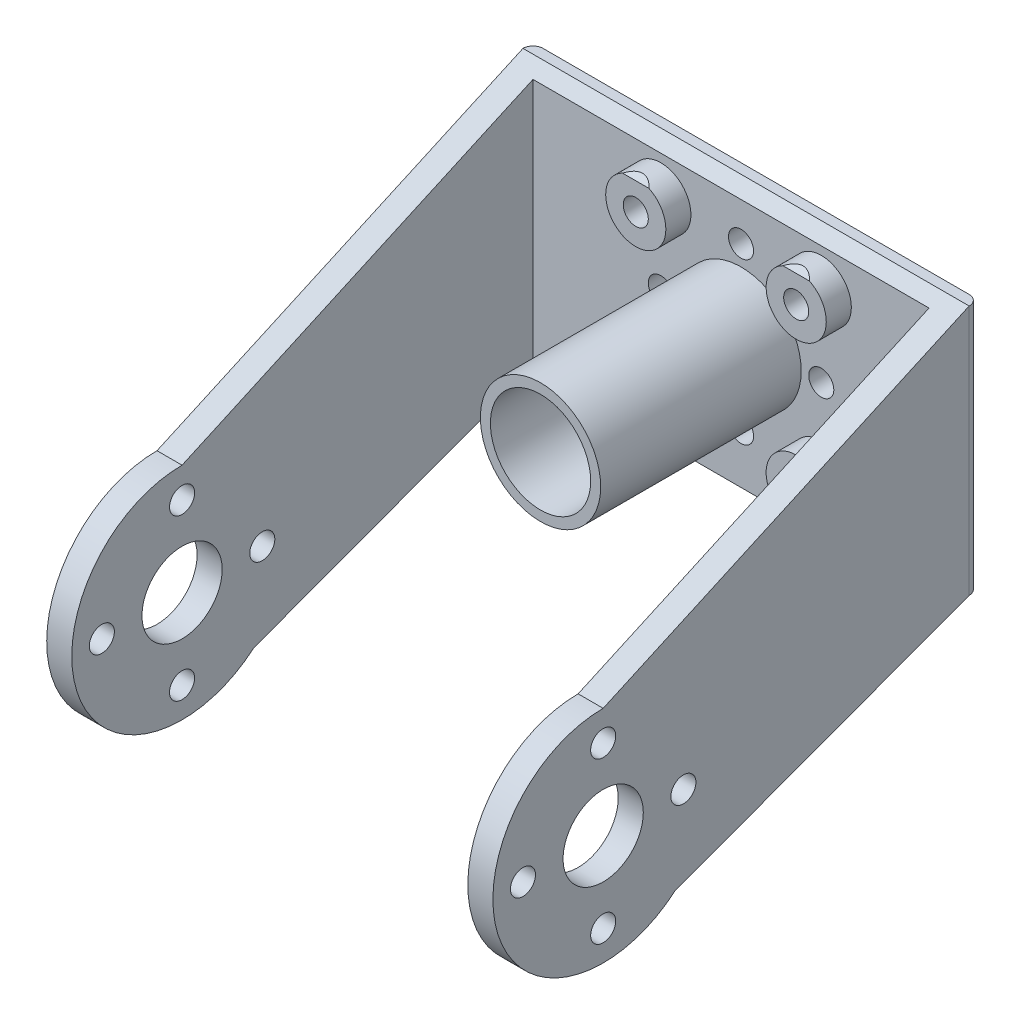
SolidWorks part; units mm, degrees
ref_plane "Front Plane" through (0, 0, 0) normal (0, 0, 1) x (1, 0, 0)
ref_plane "Top Plane" through (0, 0, 0) normal (0, 1, 0) x (1, 0, 0)
ref_plane "Right Plane" through (0, 0, 0) normal (1, 0, 0) x (0, 0, -1)
sketch "Sketch1" plane through (0, 0, 0) normal (0, 0, 1) x (1, 0, 0)
  line L1 (0, 0) -> (44.5, 0)
  line L2 (0, 0) -> (0, 40)
  line L3 (0, 40) -> (44.5, 40)
  line L4 (44.5, 0) -> (44.5, 40)
  dimension "D1" = 44.5
  dimension "D2" = 40
extrude "Boss-Extrude1" add sketch "Sketch1" along normal blind 48.5
sketch "Sketch2" plane through (0, 0, 48.5) normal (0, 0, 1) x (1, 0, 0)
  line L0 (0, 40) -> (0, 0) construction
  line L1 (2.5, 40) -> (42, 40)
  line L2 (2.5, 40) -> (2.5, 0)
  line L3 (2.5, 0) -> (42, 0)
  line L4 (42, 40) -> (42, 0)
  line L5 (0, 0) -> (44.5, 0) construction
  line L6 (44.5, 0) -> (44.5, 40) construction
  point P10 (42, 20)
  point P12 (0, 20)
  point P13 (2.5, 20)
  dimension "D1" = 2.5
  dimension "D2" = 40
  dimension "D3" = 2.5
extrude "Cut-Extrude1" cut sketch "Sketch2" against normal blind 46
fillet "Fillet1" radius 1 2 edges at (44.5, 20, 0) (0, 20, 0)
sketch "Sketch3" plane through (0, 0, 2.5) normal (0, 0, 1) x (1, 0, 0)
  line L0 (2.5, 40) -> (2.5, 0) construction
  line L3 (42, 40) -> (2.5, 40) construction
  circle A0 centre (15.25, 19.5) radius 3
  circle A1 centre (31.25, 19.5) radius 3
  circle A2 centre (31.25, 35.5) radius 3
  circle A3 centre (15.25, 35.5) radius 3
  dimension "D1" = 6
  dimension "D2" = 12.75
  dimension "D6" = 16
  dimension "D7" = 16
  dimension "D8" = 4.5
  dimension "D4" = 2
  dimension "D5" = 2
extrude "Boss-Extrude2" add sketch "Sketch3" along normal blind 2.5
sketch "Sketch5" plane through (0, 0, 5) normal (0, 0, 1) x (1, 0, 0)
  line L3 (42, 40) -> (2.5, 40) construction
  line L4 (2.5, 40) -> (2.5, 0) construction
  circle A1 centre (23.25, 35.5) radius 1.25
  circle A10 centre (31.25, 35.5) radius 1.25
  circle A11 centre (15.25, 35.5) radius 1.25
  circle A14 centre (23.25, 27.5) radius 5
  circle A15 centre (23.25, 27.5) radius 1.25 [skipped]
  circle A16 centre (31.25, 27.5) radius 1.25
  circle A17 centre (23.25, 19.5) radius 1.25
  circle A18 centre (31.25, 19.5) radius 1.25
  circle A19 centre (15.25, 27.5) radius 1.25
  circle A20 centre (15.25, 19.5) radius 1.25
  circle A21 centre (15.25, 35.5) radius 3 construction
  dimension "D1" = 2.5
  dimension "D2" = 4.5
  dimension "D7" = 3
  dimension "D8" = 3
  dimension "D9" = 8
  dimension "D4" = 10
  dimension "D3" = 12.75
  dimension "D5" = 12.5
  dimension "D6" = 20.75
extrude "Cut-Extrude5" cut sketch "Sketch5" against normal blind 6
sketch "Sketch7" plane through (44.5, 0, 0) normal (1, 0, 0) x (0, 0, -1)
  line L0 (-48.5, 0) -> (-1, 0) construction
  line L1 (-37.5, 1.5) -> (-1, 15)
  line L2 (-37.5, 23.5) -> (-1, 40)
  line L3 (-1, 0) -> (-1, 40) construction
  line L4 (-48.5, 0) -> (-48.5, 40) construction
  circle A0 centre (-37.5, 12.5) radius 4
  circle A1 centre (-37.5, 12.5) radius 11
  point P4 (0, 0)
  dimension "D2" = 8
  dimension "D4" = 22
  dimension "D1" = 12.5
  dimension "D3" = 25
  dimension "D5" = 11
extrude "Cut-Extrude7" cut sketch "Sketch7" against normal blind 44.5
sketch "Sketch8" plane through (44.5, 0, 0) normal (1, 0, 0) x (0, 0, -1)
  line L2 (-9, 23) -> (-4, 23) construction
  line L3 (-9, 32.5) -> (-9, 23) construction
  circle A7 centre (-37.5, 12.5) radius 8
  circle A8 centre (-45.5, 12.5) radius 1.25
  circle A9 centre (-37.5, 20.5) radius 1.25
  circle A11 centre (-37.5, 4.5) radius 1.25
  circle A12 centre (-29.5, 12.5) radius 1.25
  point P4 (-29.5, 12.5)
  point P9 (0, 0)
  point P11 (-27.5, 4.5)
  point P24 (-37.5, 20.5)
  point P25 (-45.5, 12.5)
  circle M8 centre (-37.5, 12.5) radius 4
  dimension "D1" = 2.5
  dimension "D6" = 2.5
  dimension "D5" = 2.5
  dimension "D3" = 16
  dimension "D2" = 16
  dimension "D4" = 2.5
extrude "Cut-Extrude8" cut sketch "Sketch8" against normal blind 44.5 contours A12 A7 A9 A8 A11 M8
sketch "Sketch9" plane through (0, 0, 1) normal (0, 0, 1) x (1, 0, 0)
  line L1 (44.5, 15) -> (0, 15)
  line L2 (44.5, 15) -> (44.5, 0)
  line L3 (44.5, 0) -> (0, 0)
  line L4 (0, 15) -> (0, 0)
extrude "Cut-Extrude9" cut sketch "Sketch9" against normal blind 10
sketch "Sketch10" plane through (0, 0, 2.5) normal (0, 0, 1) x (1, 0, 0)
  circle A0 centre (23.25, 27.5) radius 5
extrude "Extrude-Thin1" add sketch "Sketch10" along normal blind 20 thin
